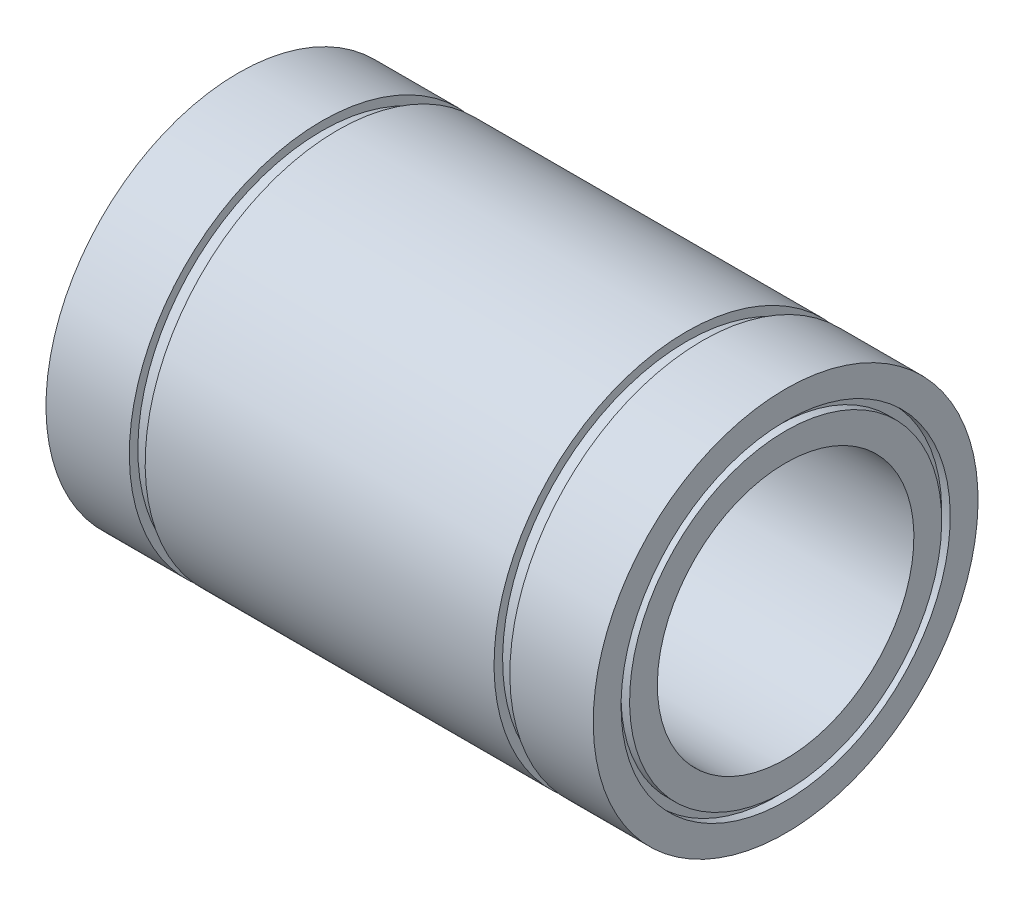
SolidWorks part; units mm, degrees
material "Ст3сп ГОСТ 535-2005"
ref_plane "Plano frontal" through (0, 0, 0) normal (0, 0, 1) x (1, 0, 0)
ref_plane "Plano superior" through (0, 0, 0) normal (0, 1, 0) x (1, 0, 0)
ref_plane "Plano direito" through (0, 0, 0) normal (1, 0, 0) x (0, 0, -1)
sketch "Esboço1" plane through (0, 0, 0) normal (0, 0, 1) x (1, 0, 0)
  line L0 (-32, 22.5) -> (-22.25, 22.5)
  line L1 (-22.25, 22.5) -> (-22.25, 21.5)
  line L2 (-22.25, 21.5) -> (-20.4, 21.5)
  line L3 (-20.4, 21.5) -> (-20.4, 22.5)
  line L4 (-20.4, 22.5) -> (20.4, 22.5)
  line L5 (20.4, 22.5) -> (20.4, 21.5)
  line L6 (20.4, 21.5) -> (22.25, 21.5)
  line L7 (22.25, 21.5) -> (22.25, 22.5)
  line L8 (22.25, 22.5) -> (32, 22.5)
  line L9 (32, 22.5) -> (32, 19.25)
  line L10 (32, 15) -> (-32, 15)
  line L11 (-32, 15) -> (-32, 18.25)
  line L12 (0, 15) -> (0, 0) construction
  line L13 (0, 0) -> (-86.5, 0) construction
  line L14 (-32, 19.25) -> (-32, 22.5)
  line L15 (-32, 19.25) -> (-31, 19.25)
  line L16 (32, 18.25) -> (32, 15)
  line L17 (-31, 19.25) -> (-31, 18.25)
  line L18 (-31, 18.25) -> (-32, 18.25)
  line L19 (32, 19.25) -> (31, 19.25)
  line L21 (32, 18.25) -> (31, 18.25)
  line L22 (31, 19.25) -> (31, 18.25)
  dimension "D1" = 64
  dimension "D2" = 44.5
  dimension "D3" = 1.85
  dimension "D4" = 30
  dimension "D5" = 45
  dimension "D6" = 43
  dimension "D7" = 1
  dimension "D8" = 1
  dimension "D9" = 1
  dimension "D10" = 1
revolve "Revolução1" add sketch "Esboço1" angle 360 about L13
